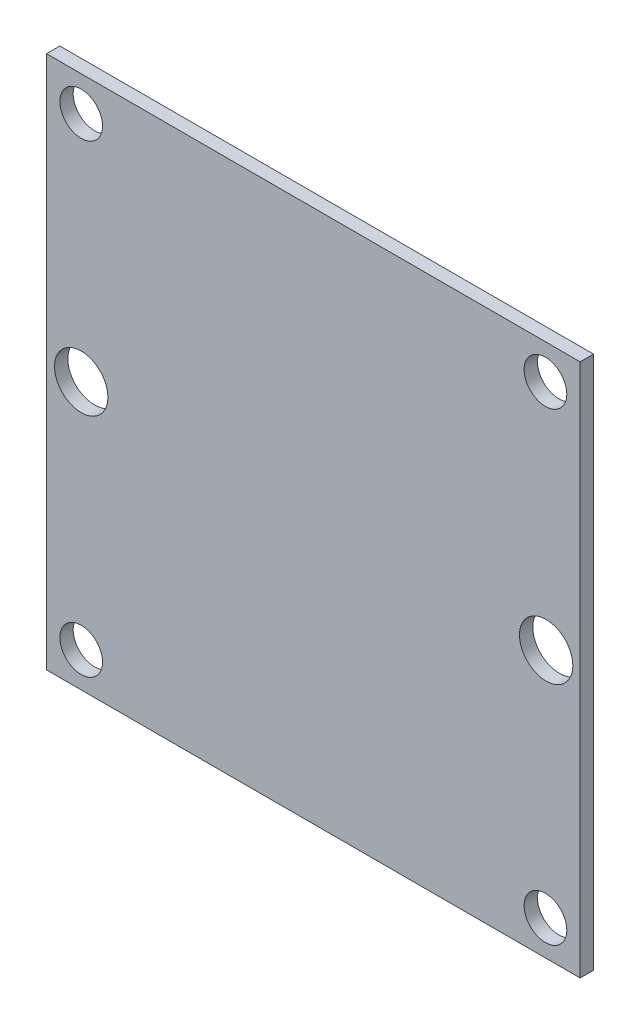
SolidWorks part; units mm, degrees
ref_plane "Front Plane" through (0, 0, 0) normal (0, 0, 1) x (1, 0, 0)
ref_plane "Top Plane" through (0, 0, 0) normal (0, 1, 0) x (1, 0, 0)
ref_plane "Right Plane" through (0, 0, 0) normal (1, 0, 0) x (0, 0, -1)
sketch "Sketch1" plane through (0, 0, 0) normal (0, 0, 1) x (1, 0, 0)
  line L1 (-20, 20) -> (20, 20)
  line L2 (-20, 20) -> (-20, -20)
  line L3 (-20, -20) -> (20, -20)
  line L4 (20, 20) -> (20, -20)
  line L5 (-20, 20) -> (20, -20) construction
  line L6 (-20, -20) -> (20, 20) construction
  point P0 (0, 0)
  dimension "D1" = 40
  dimension "D2" = 40
extrude "Boss-Extrude1" add sketch "Sketch1" along normal blind 1
sketch "Sketch2" plane through (0, 0, 1) normal (0, 0, 1) x (1, 0, 0)
  line L1 (20, 20) -> (-20, 20) construction
  line L3 (-20, -20) -> (20, -20) construction
  circle A0 centre (-17.4, -17.4) radius 1.6
  circle A1 centre (17.4, -17.4) radius 1.6
  circle A2 centre (17.4, 17.4) radius 1.6
  circle A3 centre (-17.4, 17.4) radius 1.6
  circle A5 centre (17.4507, 0) radius 2
  circle A7 centre (-17.4, 0) radius 2
  dimension "D6" = 20
  dimension "D2" = 2.6
  dimension "D4" = 2.6
extrude "Cut-Extrude1" cut sketch "Sketch2" against normal blind 10
